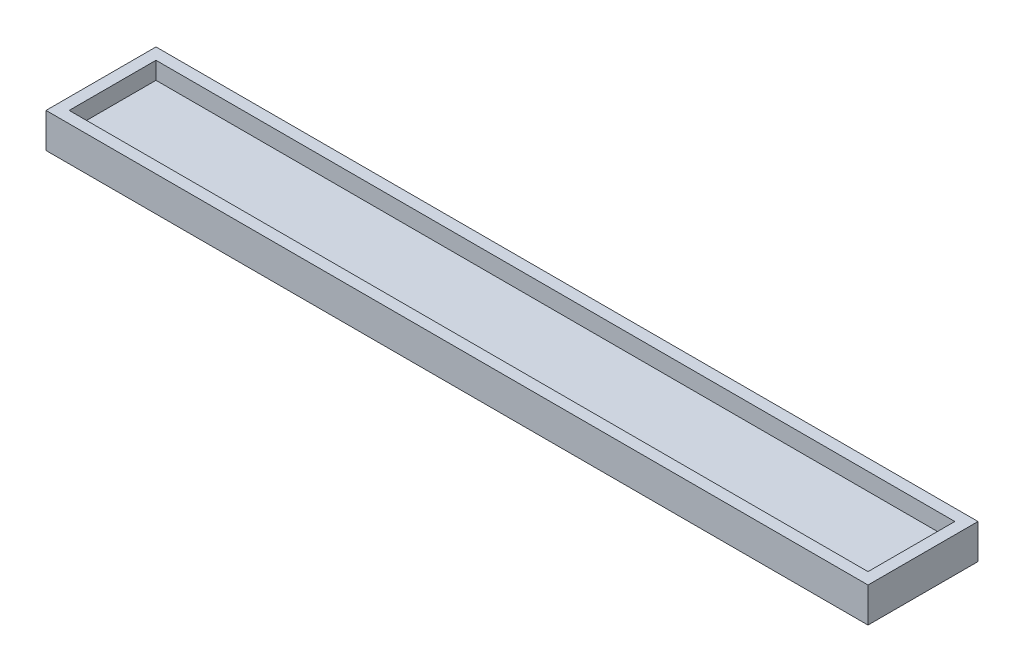
SolidWorks part; units mm, degrees
ref_plane "Front Plane" through (0, 0, 0) normal (0, 0, 1) x (1, 0, 0)
ref_plane "Top Plane" through (0, 0, 0) normal (0, 1, 0) x (1, 0, 0)
ref_plane "Right Plane" through (0, 0, 0) normal (1, 0, 0) x (0, 0, -1)
sketch "Sketch1" plane through (0, 0, 0) normal (0, 1, 0) x (1, 0, 0)
  line L1 (0, 0) -> (138, 0)
  line L2 (0, 0) -> (0, 15)
  line L3 (0, 15) -> (138, 15)
  line L4 (138, 0) -> (138, 15)
  dimension "D1" = 138
  dimension "D2" = 15
extrude "Boss-Extrude1" add sketch "Sketch1" along normal blind 3
sketch "Sketch2" plane through (0, 0, 0) normal (0, -1, 0) x (1, 0, 0)
  line L0 (-2, 2) -> (-2, -17)
  line L1 (0, 0) -> (138, 0)
  line L2 (0, 0) -> (0, -15)
  line L3 (0, -15) -> (138, -15)
  line L4 (138, 0) -> (138, -15)
  line L5 (-2, -17) -> (140, -17)
  line L6 (140, 2) -> (140, -17)
  line L7 (-2, 2) -> (140, 2)
  dimension "D1" = 2
extrude "Boss-Extrude2" add sketch "Sketch2" against normal offset from surface (6 mm away) 3 up to face at (69, 3, -7.5) offset beyond the face yes
